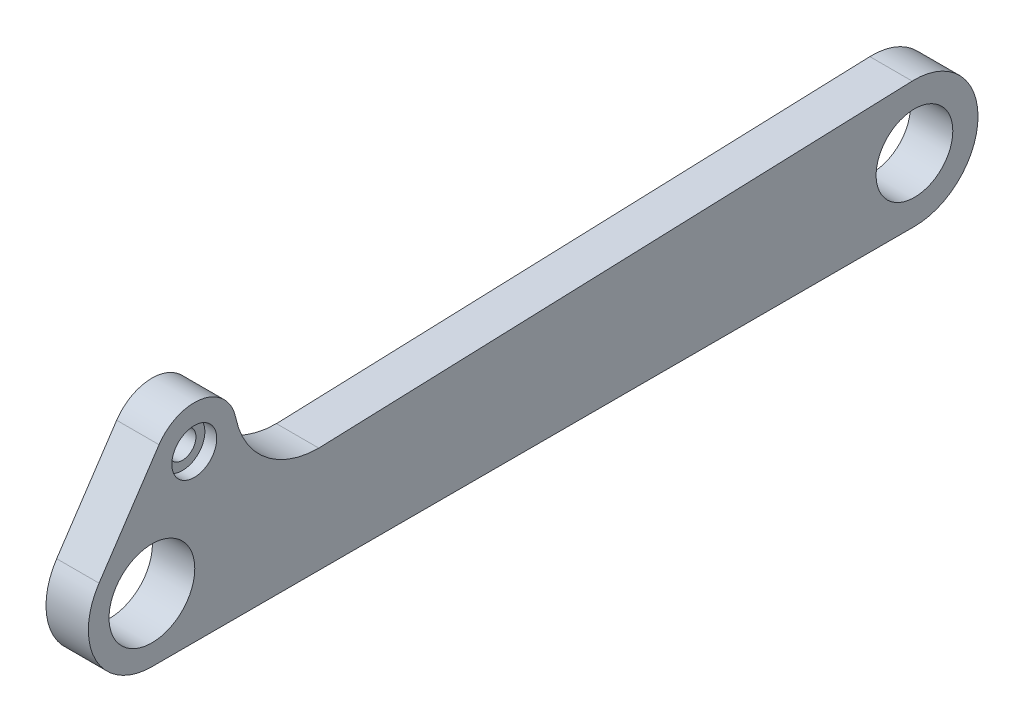
SolidWorks part; units mm, degrees
material "A-玻璃纤维"
ref_plane "前视基准面" through (0, 0, 0) normal (0, 0, 1) x (1, 0, 0)
ref_plane "上视基准面" through (0, 0, 0) normal (0, 1, 0) x (1, 0, 0)
ref_plane "右视基准面" through (0, 0, 0) normal (1, 0, 0) x (0, 0, -1)
sketch "草图1" plane through (0, 0, 0) normal (1, 0, 0) x (0, 0, -1)
  line L0 (0, 0) -> (90, 0) construction
  line L1 (0, 5) -> (90, 5)
  line L2 (0, -5) -> (90, -5)
  circle A0 centre (0, 0) radius 2.5
  arc A1 (0, 5) -> (0, -5) centre (0, 0) ccw
  arc A2 (90, -5) -> (90, 5) centre (90, 0) ccw
  circle A3 centre (90, 0) radius 2.05
  point P3 (45, 0)
  dimension "D1" = 5
  dimension "D2" = 5
  dimension "D4" = 4.1
  dimension "D3" = 90
extrude "凸台-拉伸1" add sketch "草图1" along normal blind 5
sketch "草图2" plane through (5, 0, 0) normal (1, 0, 0) x (0, 0, -1)
  line L0 (0, 0) -> (90, 0) construction
  line L1 (38, 0) -> (46.391, 10) construction
  line L2 (49.9148, 7.0432) -> (48.2004, 5)
  line L3 (90, 5) -> (0, 5) construction
  line L4 (42.8672, 12.9568) -> (36.1906, 5)
  line L5 (36.1906, 5) -> (48.2004, 5)
  circle A0 centre (46.391, 10) radius 2.5
  arc A1 (49.9148, 7.0432) -> (42.8672, 12.9568) centre (46.391, 10) ccw
  dimension "D1" = 5
  dimension "D5" = 9.2
  dimension "D2" = 50
  dimension "D3" = 10
  dimension "D4" = 52
extrude "凸台-拉伸2" add sketch "草图2" against normal up to surface (5 mm away) up to face at (0, 0, -45)
fillet "圆角1" radius 6 1 edges at (2.5, 5, -48.2004)
fillet "圆角2" radius 10 1 edges at (2.5, 5, -36.1906)
sketch "草图3" plane through (5, 0, 0) normal (1, 0, 0) x (0, 0, -1)
  line L0 (0, 0) -> (0, 14.6103) construction
  line L1 (0, 0) -> (5, 12) construction
  line L2 (-4.6154, 1.9231) -> (0.3846, 13.9231)
  line L3 (7.5, 5) -> (9.6154, 10.0769)
  line L4 (31.5275, 5) -> (0, 5) construction
  line L5 (7.5, 5) -> (0, 5)
  circle A0 centre (5, 12) radius 1.6
  arc A1 (9.6154, 10.0769) -> (0.3846, 13.9231) centre (5, 12) ccw
  arc A2 (0, 5) -> (0, -5) centre (0, 0) ccw construction
  arc A3 (0, 5) -> (-4.6154, 1.9231) centre (0, 0) ccw
  dimension "D1" = 3.2
  dimension "D4" = 10
  dimension "D2" = 12
  dimension "D3" = 5
extrude "凸台-拉伸3" add sketch "草图3" against normal up to surface (5 mm away) up to face at (0, 4.7395, -44.6313)
fillet "圆角3" radius 10 1 edges at (2.5, 5, -7.5)
sketch "草图4" plane through (5, 0, 0) normal (1, 0, 0) x (0, 0, -1)
  line L0 (25.6122, 5) -> (73.4719, 5)
  line L1 (31.5275, 5) -> (19.6969, 5) construction
  line L2 (90, 5) -> (56.9437, 5) construction
  line L3 (73.4719, 5) -> (73.4719, 20)
  line L4 (73.4719, 20) -> (25.6122, 20)
  line L5 (25.6122, 20) -> (25.6122, 5)
  dimension "D1" = 15
extrude "切除-拉伸1" cut sketch "草图4" against normal through all
sketch "草图6" plane through (5, 0, 0) normal (1, 0, 0) x (0, 0, -1)
  circle A0 centre (5, 12) radius 2.65
  dimension "D1" = 5.3
extrude "切除-拉伸2" cut sketch "草图6" against normal blind 1.4
sketch "草图10" plane through (5, 0, 0) normal (1, 0, 0) x (0, 0, -1)
  line L0 (89.733, 7.4952) -> (19.6969, 5)
  line L2 (90, -7.5) -> (0, -7.5)
  line L7 (-6.2391, 4.1621) -> (0.8406, 14.7748)
  line L9 (90, 5) -> (19.6969, 5)
  line L10 (0.3846, 13.9231) -> (-4.6154, 1.9231)
  line L11 (0, -5) -> (90, -5)
  line L12 (90, 5) -> (19.6969, 5)
  line L13 (0.3846, 13.9231) -> (-4.6154, 1.9231)
  line L14 (0, -5) -> (90, -5)
  arc A0 (90, -7.5) -> (89.733, 7.4952) centre (90, 0) ccw
  arc A1 (-6.2391, 4.1621) -> (0, -7.5) centre (0, 0) ccw
  arc A2 (9.899, 13) -> (0.3846, 13.9231) centre (5, 12) ccw construction
  circle A4 centre (90, 0) radius 2.05 construction
  arc A13 (9.899, 13) -> (19.6969, 5) centre (19.6969, 15) ccw
  arc A14 (9.899, 13) -> (0.3846, 13.9231) centre (5, 12) ccw
  arc A15 (-4.6154, 1.9231) -> (0, -5) centre (0, 0) ccw
  arc A16 (90, -5) -> (90, 5) centre (90, 0) ccw
  arc A18 (0.8406, 14.7748) -> (0.3846, 13.9231) centre (5, 12) ccw
  arc A19 (-4.6154, 1.9231) -> (0, -5) centre (0, 0) ccw
  arc A20 (90, -5) -> (90, 5) centre (90, 0) ccw
  dimension "D3" = 15
  dimension "D1" = 0
extrude "凸台-拉伸5" add sketch "草图10" against normal up to surface (5 mm away) up to face at (0, 4.1972, -29.6326)
sketch "草图11" plane through (5, 0, 0) normal (1, 0, 0) x (0, 0, -1)
  circle A0 centre (90, 0) radius 4.525
  dimension "D1" = 9.05
extrude "切除-拉伸4" cut sketch "草图11" against normal through all
sketch "草图13" plane through (5, 0, 0) normal (1, 0, 0) x (0, 0, -1)
  circle A0 centre (0, 0) radius 5.06
  dimension "D1" = 10.12
extrude "切除-拉伸5" cut sketch "草图13" against normal up to surface (5 mm away) up to face at (0, 0, -94.525)
